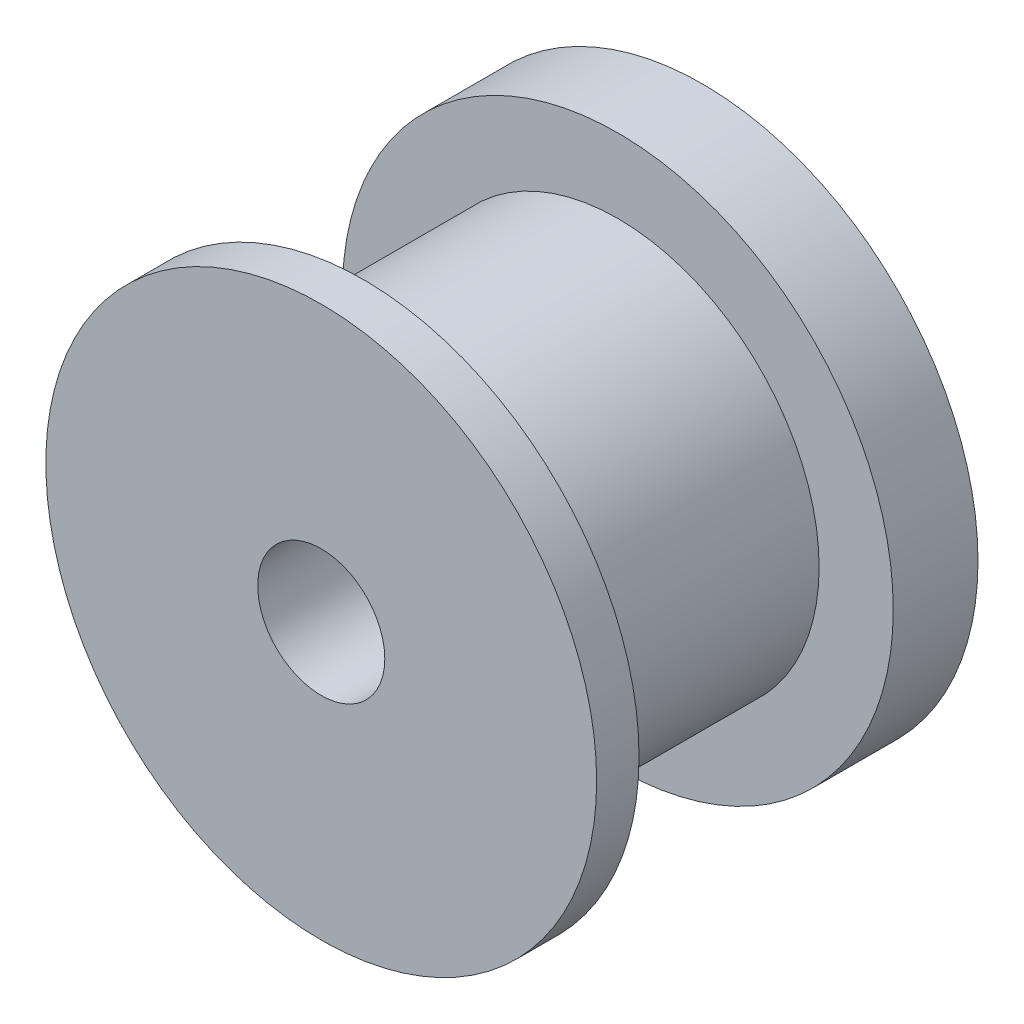
SolidWorks part; units mm, degrees
ref_plane "前视基准面" through (0, 0, 0) normal (0, 0, 1) x (1, 0, 0)
ref_plane "上视基准面" through (0, 0, 0) normal (0, 1, 0) x (1, 0, 0)
ref_plane "右视基准面" through (0, 0, 0) normal (1, 0, 0) x (0, 0, -1)
sketch "草图1" plane through (0, 0, 0) normal (0, 0, 1) x (1, 0, 0)
  circle A0 centre (0, 0) radius 6.5
  dimension "D1" = 13
extrude "凸台-拉伸1" add sketch "草图1" along normal blind 2
sketch "草图2" plane through (0, 0, 2) normal (0, 0, 1) x (1, 0, 0)
  circle A0 centre (0, 0) radius 4.75
  dimension "D1" = 9.5
extrude "凸台-拉伸2" add sketch "草图2" along normal blind 6
sketch "草图3" plane through (0, 0, 8) normal (0, 0, 1) x (1, 0, 0)
  circle A0 centre (0, 0) radius 6.5
extrude "凸台-拉伸3" add sketch "草图3" along normal blind 1
sketch "草图4" plane through (0, 0, 9) normal (0, 0, 1) x (1, 0, 0)
  circle A0 centre (0, 0) radius 1.5
  dimension "D1" = 3
extrude "切除-拉伸1" cut sketch "草图4" against normal through all
